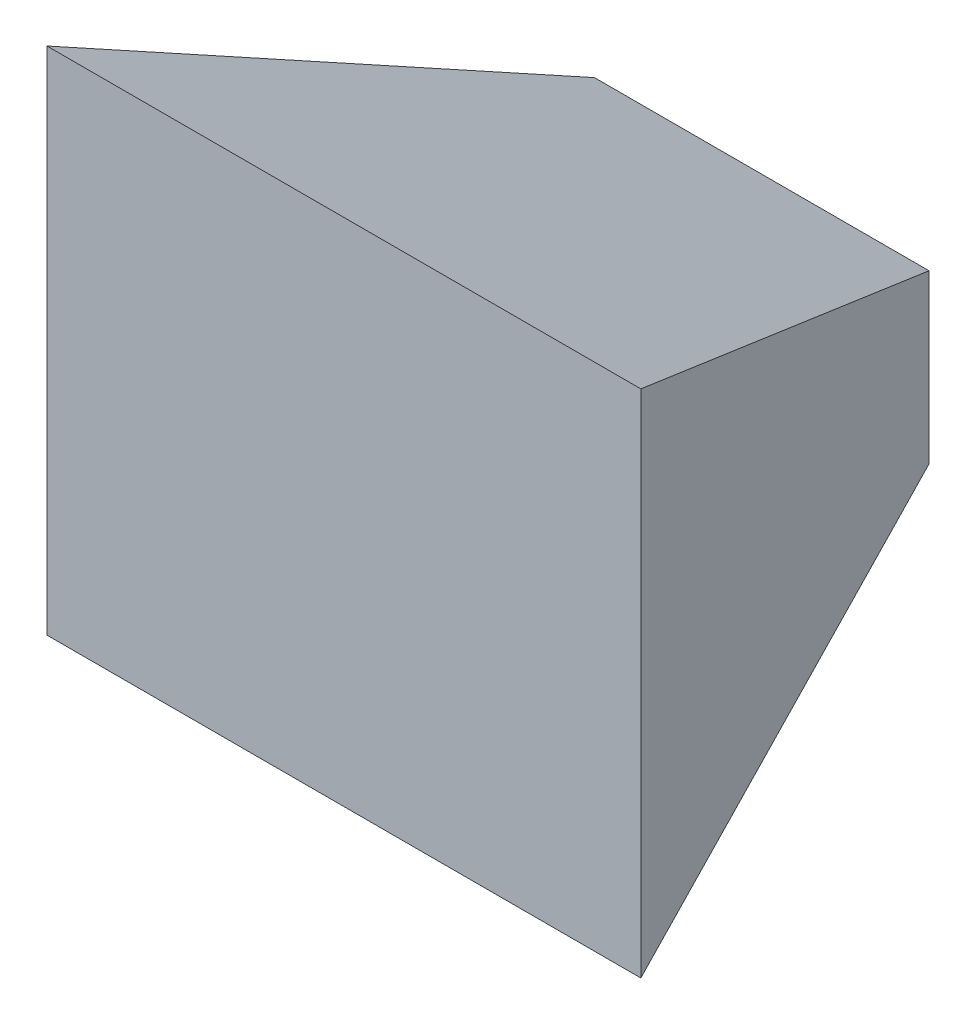
SolidWorks part; units mm, degrees
ref_plane "Front Plane" through (0, 0, 0) normal (0, 0, 1) x (1, 0, 0)
ref_plane "Top Plane" through (0, 0, 0) normal (0, 1, 0) x (1, 0, 0)
ref_plane "Right Plane" through (0, 0, 0) normal (1, 0, 0) x (0, 0, -1)
sketch "Sketch1" plane through (0, 0, 0) normal (0, 0, 1) x (1, 0, 0)
  line L5 (-177.5, -152.5) -> (177.5, -152.5)
  line L6 (-177.5, -152.5) -> (-177.5, 152.5)
  line L7 (-177.5, 152.5) -> (177.5, 152.5)
  line L8 (177.5, -152.5) -> (177.5, 152.5)
  line L9 (-177.5, -152.5) -> (177.5, 152.5) construction
  line L10 (-177.5, 152.5) -> (177.5, -152.5) construction
  point P0 (0, 0)
  dimension "D1" = 305
  dimension "D2" = 355
sketch "Sketch2" plane through (0, 0, 0) normal (1, 0, 0) x (0, 0, -1)
  line L0 (0, 152.5) -> (0, -152.5) construction
  line L1 (0, 152.5) -> (0, -152.5)
  line L2 (0, 0) -> (249.7874, 0) construction
  line L3 (249.7874, -50) -> (249.7874, 50)
  line L4 (249.7874, 50) -> (0, 152.5)
  line L5 (249.7874, -50) -> (0, -152.5)
  point P8 (249.7874, 0)
  dimension "D1" = 305
  dimension "D2" = 100
  dimension "D3" = 270
sketch "Sketch3" plane through (0, 0, 0) normal (0, 1, 0) x (1, 0, 0)
  line L0 (-177.5, 0) -> (177.5, 0) construction
  line L1 (-177.5, 0) -> (177.5, 0)
  line L2 (-100, 249.7874) -> (100, 249.7874)
  line L3 (100, 249.7874) -> (177.5, 0)
  line L4 (-100, 249.7874) -> (-177.5, 0)
  line L5 (177.5, 0) -> (177.5, 249.7874)
  line L6 (177.5, 249.7874) -> (100, 249.7874)
  line L7 (-177.5, 0) -> (-177.5, 249.7874)
  line L8 (-177.5, 249.7874) -> (-100, 249.7874)
  point P2 (0, 249.7874)
  point P7 (0, 249.7874)
  dimension "D1" = 200
extrude "Boss-Extrude2" add sketch "Sketch2" along normal mid plane 355
extrude "Cut-Extrude1" cut sketch "Sketch3" against normal mid plane 305 contours L8 L7 L4 | L5 L6 L3
